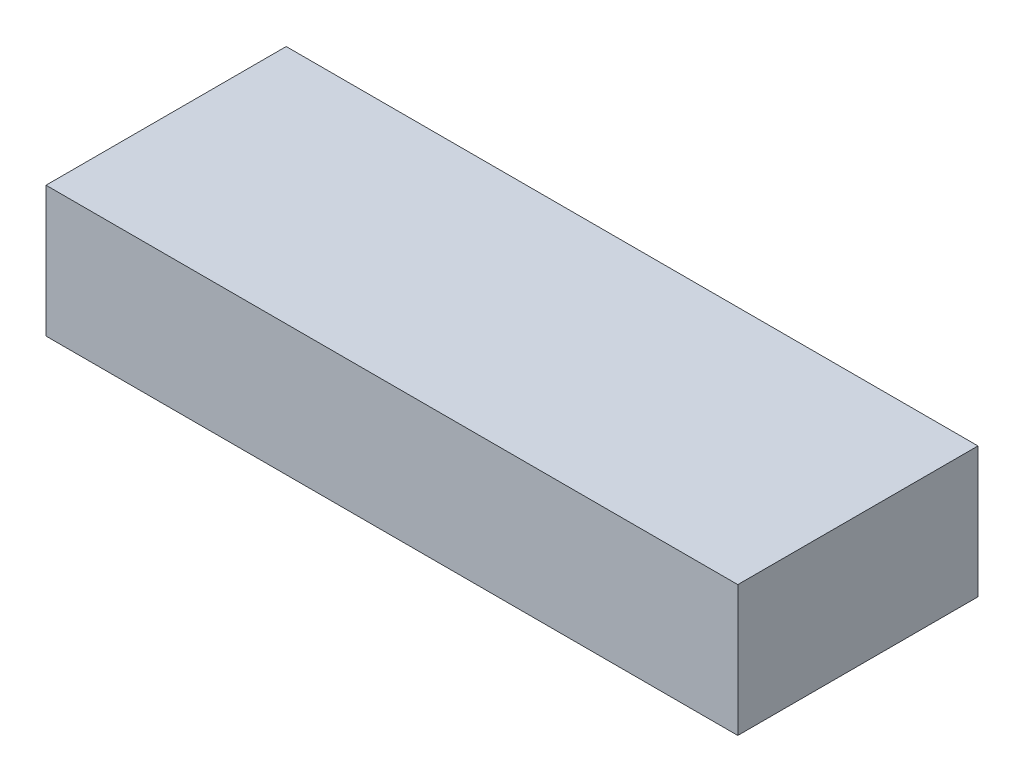
SolidWorks part; units mm, degrees
ref_plane "Front Plane" through (0, 0, 0) normal (0, 0, 1) x (1, 0, 0)
ref_plane "Top Plane" through (0, 0, 0) normal (0, 1, 0) x (1, 0, 0)
ref_plane "Right Plane" through (0, 0, 0) normal (1, 0, 0) x (0, 0, -1)
sketch "Sketch1" plane through (0, 0, 0) normal (0, 1, 0) x (1, 0, 0)
  line L1 (-36, -12.5) -> (36, -12.5)
  line L2 (-36, -12.5) -> (-36, 12.5)
  line L3 (-36, 12.5) -> (36, 12.5)
  line L4 (36, -12.5) -> (36, 12.5)
  line L5 (-36, -12.5) -> (36, 12.5) construction
  line L6 (-36, 12.5) -> (36, -12.5) construction
  point P0 (0, 0)
  dimension "D1" = 72
  dimension "D2" = 25
extrude "Boss-Extrude1" add sketch "Sketch1" along normal blind 13.6
